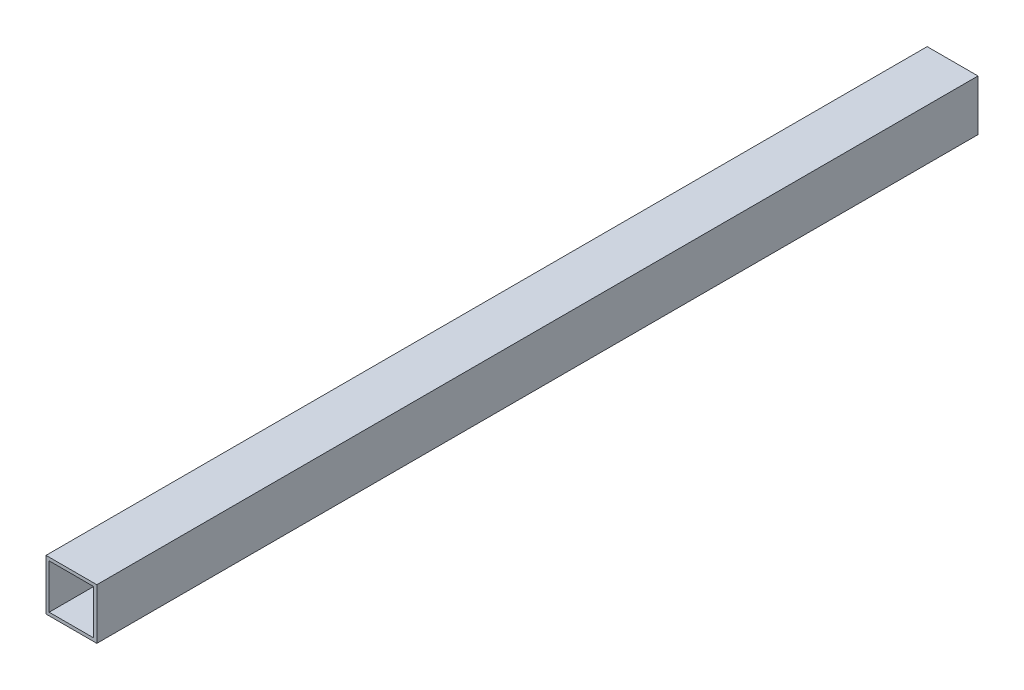
SolidWorks part; units mm, degrees
ref_plane "Front Plane" through (0, 0, 0) normal (0, 0, 1) x (1, 0, 0)
ref_plane "Top Plane" through (0, 0, 0) normal (0, 1, 0) x (1, 0, 0)
ref_plane "Right Plane" through (0, 0, 0) normal (1, 0, 0) x (0, 0, -1)
sketch "Sketch1" plane through (0, 0, 0) normal (0, 0, 1) x (1, 0, 0)
  line L1 (-38.1, -38.1) -> (38.1, -38.1)
  line L2 (-38.1, -38.1) -> (-38.1, 38.1)
  line L3 (-38.1, 38.1) -> (38.1, 38.1)
  line L4 (38.1, -38.1) -> (38.1, 38.1)
  line L5 (-38.1, -38.1) -> (38.1, 38.1) construction
  line L6 (-38.1, 38.1) -> (38.1, -38.1) construction
  line L7 (-33.3375, -33.3375) -> (33.3375, -33.3375)
  line L8 (-33.3375, -33.3375) -> (-33.3375, 33.3375)
  line L9 (-33.3375, 33.3375) -> (33.3375, 33.3375)
  line L10 (33.3375, -33.3375) -> (33.3375, 33.3375)
  line L11 (-33.3375, -33.3375) -> (33.3375, 33.3375) construction
  line L12 (-33.3375, 33.3375) -> (33.3375, -33.3375) construction
  point P0 (0, 0)
  point P6 (0, 0)
  dimension "D1" = 4.7625
  dimension "D2" = 76.2
extrude "Boss-Extrude1" add sketch "Sketch1" along normal blind 1320.8
